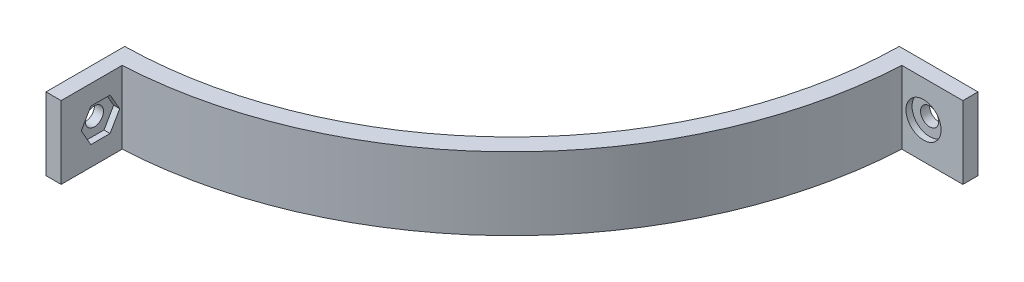
SolidWorks part; units mm, degrees
ref_plane "Front Plane" through (0, 0, 0) normal (0, 0, 1) x (1, 0, 0)
ref_plane "Top Plane" through (0, 0, 0) normal (0, 1, 0) x (1, 0, 0)
ref_plane "Right Plane" through (0, 0, 0) normal (1, 0, 0) x (0, 0, -1)
sketch "Sketch1" plane through (0, 0, 0) normal (0, 1, 0) x (1, 0, 0)
  circle A0 centre (0, 0) radius 65
  circle A1 centre (0, 0) radius 68
  dimension "D1" = 130
  dimension "D2" = 136
extrude "Boss-Extrude1" add sketch "Sketch1" along normal mid plane 50
ref_plane "Plane1" through (68, 0, 0) normal (1, 0, 0) x (0, 0, -1)
sketch "Sketch2" plane through (68, 0, 0) normal (1, 0, 0) x (0, 0, -1)
  line L0 (-68, -25) -> (68, -25) construction
  line L1 (-3.5, 25) -> (3.5, 25)
  line L2 (-3.5, 25) -> (-3.5, -25)
  line L3 (-3.5, -25) -> (3.5, -25)
  line L4 (3.5, 25) -> (3.5, -25)
  line L5 (-3.5, 25) -> (3.5, -25) construction
  line L6 (-3.5, -25) -> (3.5, 25) construction
  point P0 (0, 0)
  dimension "D1" = 7
extrude "Boss-Extrude2" add sketch "Sketch2" along normal blind 10 and the other way up to body separate body
sketch "Sketch3" plane through (78, 0, 0) normal (1, 0, 0) x (0, 0, -1)
  line L0 (-3.5, -25) -> (3.5, -25) construction
  line L1 (-1, 25) -> (1, 25)
  line L2 (-1, 25) -> (-1, -25)
  line L3 (-1, -25) -> (1, -25)
  line L4 (1, 25) -> (1, -25)
  line L5 (-1, 25) -> (1, -25) construction
  line L6 (-1, -25) -> (1, 25) construction
  point P0 (0, 0)
  dimension "D1" = 2
extrude "Cut-Extrude1" cut sketch "Sketch3" against normal blind 10
pattern_circular "CirPattern2" count 4 over 360 about axis through (0, 0, 0) along (0, 1, 0) of "Cut-Extrude1", "Boss-Extrude2"
sketch "Sketch7" plane through (0, 0, 3.5) normal (0, 0, 1) x (1, 0, 0)
  line L0 (78, 25) -> (78, -25) construction
  line L1 (78, 25) -> (67.9099, 25) construction
  circle A0 centre (71.5, 19) radius 2.9
  dimension "D2" = 6
  dimension "5.8" = 5.8
  dimension "D1" = 6.5
extrude "Cut-Extrude4" cut sketch "Sketch7" against normal blind 1
sketch "Sketch8" plane through (0, 0, -3.5) normal (0, 0, -1) x (-1, 0, 0)
  line L0 (-78, 25) -> (-67.9099, 25) construction
  line L1 (-69.9123, 16.25) -> (-68.3246, 19)
  line L2 (-68.3246, 19) -> (-69.9123, 21.75)
  line L3 (-69.9123, 21.75) -> (-73.0877, 21.75)
  line L4 (-73.0877, 21.75) -> (-74.6754, 19)
  line L5 (-74.6754, 19) -> (-73.0877, 16.25)
  line L6 (-73.0877, 16.25) -> (-69.9123, 16.25)
  line L7 (-78, -25) -> (-78, 25) construction
  circle A0 centre (-71.5, 19) radius 2.75 construction
  dimension "D1" = 6
  dimension "D2" = 6.5
  dimension "D3" = 5.5
extrude "Cut-Extrude5" cut sketch "Sketch8" against normal blind 1
sketch "Sketch9" plane through (0, 0, 2.5) normal (0, 0, 1) x (1, 0, 0)
  circle A0 centre (71.5, 19) radius 1.5
  dimension "D1" = 3
extrude "Cut-Extrude6" cut sketch "Sketch9" against normal through all
mirror "Mirror1" about plane through (0, 0, 0) normal (0, 1, 0) of "Cut-Extrude6", "Cut-Extrude4", "Cut-Extrude5"
pattern_circular "CirPattern3" count 4 over 360 about axis through (0, 0, 0) along (0, 1, 0) of "Mirror1", "Cut-Extrude4", "Cut-Extrude5", "Cut-Extrude6"
sketch "Sketch10" plane through (0, 0, 0) normal (0, 1, 0) x (1, 0, 0)
  line L1 (-86, 92.0497) -> (86.3223, 92.0497)
  line L2 (-86, 92.0497) -> (-86, -89.3457)
  line L3 (-86, -89.3457) -> (86.3223, -89.3457)
  line L4 (86.3223, 92.0497) -> (86.3223, -89.3457)
  point P4 (86.3223, 92.0497)
  point P5 (-86, -89.3457)
extrude "Cut-Extrude7" cut sketch "Sketch10" against normal through all and the other way blind 13
sketch "Sketch4" plane through (0, 0, 0) normal (0, 0, 1) x (1, 0, 0)
  line L1 (-102.6637, -40.9209) -> (102.1327, -40.9209)
  line L2 (-102.6637, -40.9209) -> (-102.6637, 39.6925)
  line L3 (-102.6637, 39.6925) -> (102.1327, 39.6925)
  line L4 (102.1327, -40.9209) -> (102.1327, 39.6925)
extrude "Cut-Extrude2" cut sketch "Sketch4" against normal through all
sketch "Sketch5" plane through (0, 0, 0) normal (1, 0, 0) x (0, 0, -1)
  line L1 (-80.5883, -49.8416) -> (52.4174, -49.8416)
  line L2 (-80.5883, -49.8416) -> (-80.5883, 51.5208)
  line L3 (-80.5883, 51.5208) -> (52.4174, 51.5208)
  line L4 (52.4174, -49.8416) -> (52.4174, 51.5208)
extrude "Cut-Extrude3" cut sketch "Sketch5" against normal through all
sketch "Sketch11" plane through (68, 0, 0) normal (1, 0, 0) x (0, 0, -1)
  line L4 (-1, 13) -> (0, 13)
  line L5 (0, 13) -> (0, 25)
  line L6 (0, 25) -> (-1, 25)
  line L7 (-1, 25) -> (-1, 13)
  line L8 (-1, 13) -> (0, 13)
  line L10 (0, 25) -> (-1, 25)
  line L11 (-1, 25) -> (-1, 13)
  line L13 (0, 13) -> (0, 25)
  dimension "D1" = 0
extrude "Cut-Extrude8" cut sketch "Sketch11" against normal through all both and the other way through all
sketch "Sketch12" plane through (0, 0, 68) normal (0, 0, 1) x (1, 0, 0)
  line L4 (1, 25) -> (0, 25)
  line L5 (0, 25) -> (0, 13)
  line L6 (0, 13) -> (1, 13)
  line L7 (1, 13) -> (1, 25)
  line L8 (1, 25) -> (0, 25)
  line L9 (0, 25) -> (0, 13)
  line L11 (1, 13) -> (1, 25)
  line L13 (0, 13) -> (1, 13)
  dimension "D1" = 0
extrude "Cut-Extrude9" cut sketch "Sketch12" against normal blind 10
